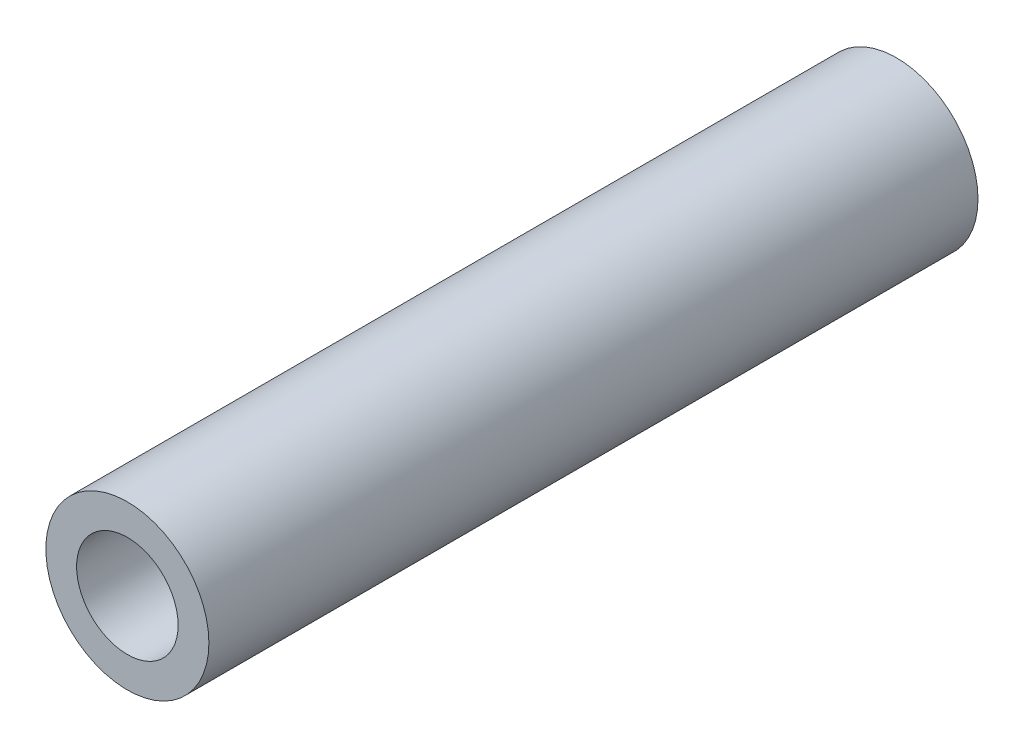
SolidWorks part; units mm, degrees
ref_plane "Front Plane" through (0, 0, 0) normal (0, 0, 1) x (1, 0, 0)
ref_plane "Top Plane" through (0, 0, 0) normal (0, 1, 0) x (1, 0, 0)
ref_plane "Right Plane" through (0, 0, 0) normal (1, 0, 0) x (0, 0, -1)
sketch "Sketch1" plane through (0, 0, 0) normal (0, 0, 1) x (1, 0, 0)
  circle A0 centre (0, 0) radius 1.65
  circle A1 centre (0, 0) radius 2.65
  dimension "D1" = 3.3
  dimension "D2" = 1
extrude "Boss-Extrude1" add sketch "Sketch1" along normal blind 25
